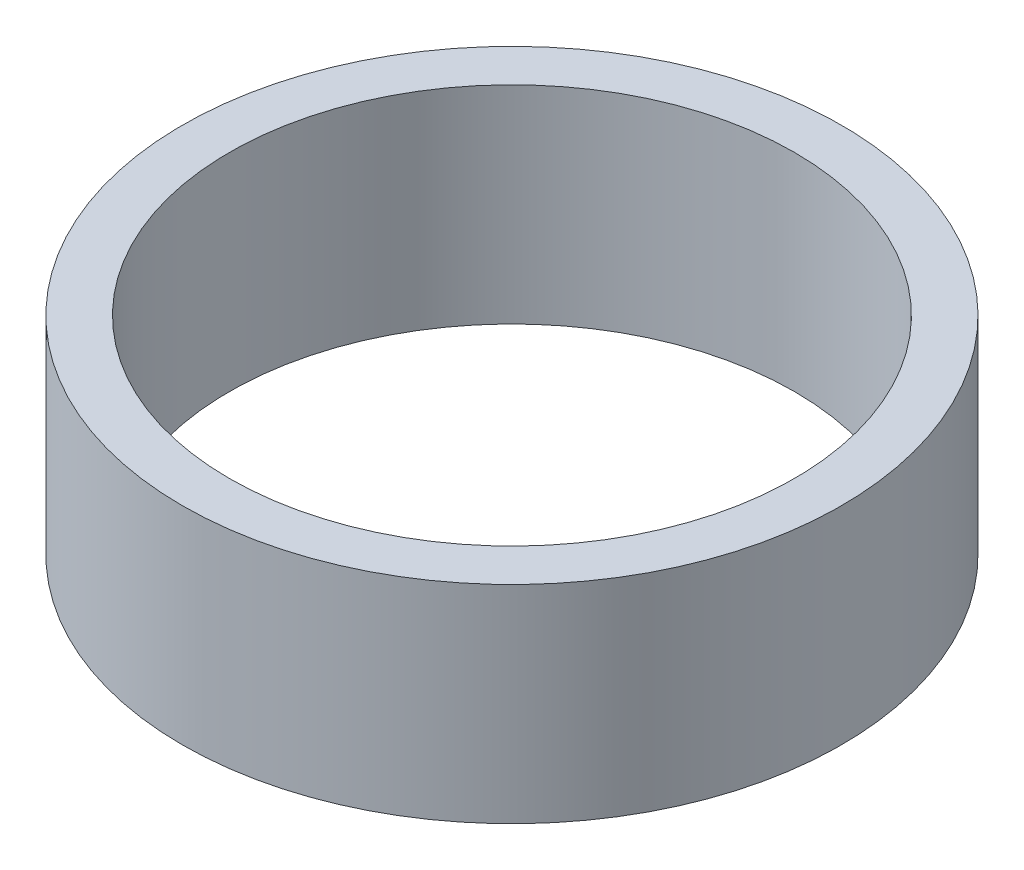
SolidWorks part; units mm, degrees
ref_plane "Front Plane" through (0, 0, 0) normal (0, 0, 1) x (1, 0, 0)
ref_plane "Top Plane" through (0, 0, 0) normal (0, 1, 0) x (1, 0, 0)
ref_plane "Right Plane" through (0, 0, 0) normal (1, 0, 0) x (0, 0, -1)
sketch "Sketch1" plane through (0, 0, 0) normal (0, 1, 0) x (1, 0, 0)
  circle A0 centre (0, 0) radius 7
  circle A1 centre (0, 0) radius 6
  dimension "D1" = 12
  dimension "D2" = 14
extrude "Boss-Extrude1" add sketch "Sketch1" along normal blind 4.4 contours A0
